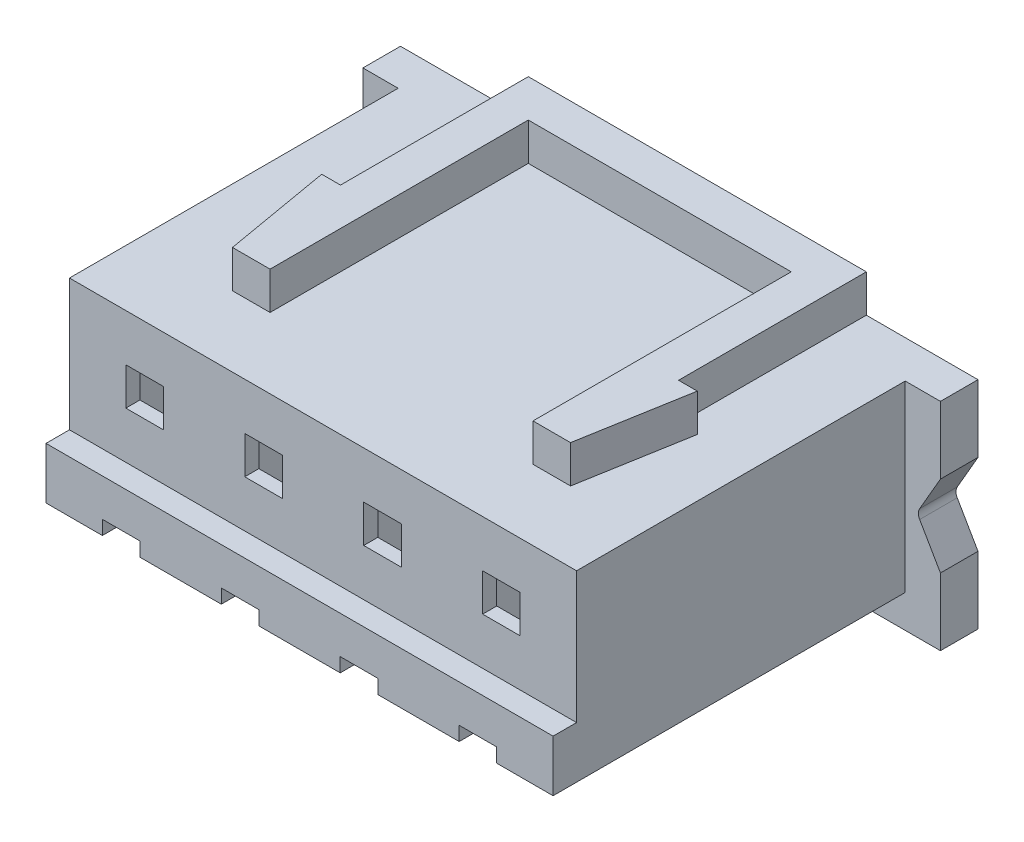
SolidWorks part; units mm, degrees
ref_plane "Front Plane" through (0, 0, 0) normal (0, 0, 1) x (1, 0, 0)
ref_plane "Top Plane" through (0, 0, 0) normal (0, 1, 0) x (1, 0, 0)
ref_plane "Right Plane" through (0, 0, 0) normal (1, 0, 0) x (0, 0, -1)
sketch "Sketch1" plane through (0, 0, 0) normal (0, 0, 1) x (1, 0, 0)
  line L1 (-5.4, -2.15) -> (5.4, -2.15)
  line L2 (-5.4, -2.15) -> (-5.4, 2.15)
  line L3 (-5.4, 2.15) -> (5.4, 2.15)
  line L4 (5.4, -2.15) -> (5.4, 2.15)
  line L5 (-5.4, -2.15) -> (5.4, 2.15) construction
  line L6 (-5.4, 2.15) -> (5.4, -2.15) construction
  point P0 (0, 0)
  dimension "D1" = 4.3
  dimension "D2" = 10.8
extrude "Boss-Extrude1" add sketch "Sketch1" along normal blind 7
sketch "Sketch2" plane through (0, 0, 0) normal (0, 0, -1) x (-1, 0, 0)
  line L0 (0, 0) -> (0, 2.15) construction
  line L1 (-6.15, 2.15) -> (6.15, 2.15)
  line L2 (-6.15, 2.15) -> (-6.15, -2.45)
  line L3 (-6.15, -2.45) -> (6.15, -2.45)
  line L4 (6.15, 2.15) -> (6.15, -2.45)
  dimension "D1" = 12.3
  dimension "D2" = 4.6
extrude "Boss-Extrude2" add sketch "Sketch2" along normal blind 0.8
sketch "Sketch3" plane through (0, 0, 0) normal (0, 0, 1) x (1, 0, 0)
  line L1 (6.15, 2.15) -> (6.15, -2.45) construction
  line L2 (5.65, -0.15) -> (6.15, -1.016)
  line L3 (5.65, -0.15) -> (6.15, 0.716)
  line L4 (6.15, -0.15) -> (5.65, -0.15) construction
  line L5 (6.15, 0.716) -> (6.15, -1.016)
  dimension "D1" = 60
  dimension "D2" = 0.5
  dimension "D3" = 60
extrude "Cut-Extrude1" cut sketch "Sketch3" against normal blind 1
fillet "Fillet1" radius 0.2 1 edges at (5.65, -0.15, -0.4)
sketch "Sketch4" plane through (0, 0, 7) normal (0, 0, 1) x (1, 0, 0)
  line L0 (-5.4, 2.15) -> (-5.4, -2.15) construction
  line L1 (-5.4, -0.65) -> (5.4, -0.65)
  line L2 (-5.4, -0.65) -> (-5.4, -2.15)
  line L3 (-5.4, -2.15) -> (5.4, -2.15)
  line L4 (5.4, -0.65) -> (5.4, -2.15)
  dimension "D1" = 1.5
extrude "Boss-Extrude3" add sketch "Sketch4" along normal blind 0.5
sketch "Sketch5" plane through (0, 0, 7.5) normal (0, 0, 1) x (1, 0, 0)
  line L0 (-5.4, -2.15) -> (5.4, -2.15) construction
  line L1 (-4.2, -1.45) -> (-3.4, -1.45)
  line L2 (-4.2, -1.45) -> (-4.2, -2.15)
  line L3 (-4.2, -2.15) -> (-3.4, -2.15)
  line L4 (-3.4, -1.45) -> (-3.4, -2.15)
  line L5 (-5.4, -0.65) -> (-5.4, -2.15) construction
  line L6 (-1.6667, -1.45) -> (-0.8667, -1.45)
  line L7 (-0.8667, -1.45) -> (-0.8667, -2.15)
  line L8 (-1.6667, -1.45) -> (-1.6667, -2.15)
  line L9 (-1.6667, -2.15) -> (-0.8667, -2.15)
  line L10 (0.8667, -1.45) -> (1.6667, -1.45)
  line L11 (1.6667, -1.45) -> (1.6667, -2.15)
  line L12 (0.8667, -1.45) -> (0.8667, -2.15)
  line L13 (0.8667, -2.15) -> (1.6667, -2.15)
  line L14 (3.4, -1.45) -> (4.2, -1.45)
  line L15 (4.2, -1.45) -> (4.2, -2.15)
  line L16 (3.4, -1.45) -> (3.4, -2.15)
  line L17 (3.4, -2.15) -> (4.2, -2.15)
  line L18 (5.4, -2.15) -> (5.4, -0.65) construction
  line L19 (-5.4, -2.15) -> (5.4, -2.15) construction
  dimension "D1" = 0.8
  dimension "D2" = 1.2
  dimension "D3" = 0.7
  dimension "D5" = 1.2
  dimension "D6" = 0.7
  dimension "D4" = 4
extrude "Cut-Extrude2" cut sketch "Sketch5" against normal blind 3.2
sketch "Sketch6" plane through (0, 0, 7) normal (0, 0, 1) x (1, 0, 0)
  line L0 (-5.4, 2.15) -> (-5.4, -0.65) construction
  line L1 (-4.2, 1.15) -> (-3.4, 1.15)
  line L2 (-4.2, 1.15) -> (-4.2, 0.35)
  line L3 (-4.2, 0.35) -> (-3.4, 0.35)
  line L4 (-3.4, 1.15) -> (-3.4, 0.35)
  line L5 (-1.6667, 0.35) -> (-0.8667, 0.35)
  line L6 (-0.8667, 1.15) -> (-0.8667, 0.35)
  line L7 (-1.6667, 1.15) -> (-0.8667, 1.15)
  line L8 (-1.6667, 1.15) -> (-1.6667, 0.35)
  line L9 (0.8667, 0.35) -> (1.6667, 0.35)
  line L10 (1.6667, 1.15) -> (1.6667, 0.35)
  line L11 (0.8667, 1.15) -> (1.6667, 1.15)
  line L12 (0.8667, 1.15) -> (0.8667, 0.35)
  line L13 (3.4, 0.35) -> (4.2, 0.35)
  line L14 (4.2, 1.15) -> (4.2, 0.35)
  line L15 (3.4, 1.15) -> (4.2, 1.15)
  line L16 (3.4, 1.15) -> (3.4, 0.35)
  line L17 (5.4, -2.15) -> (5.4, 2.15) construction
  line L18 (5.4, 2.15) -> (-5.4, 2.15) construction
  dimension "D1" = 0.8
  dimension "D2" = 0.8
  dimension "D3" = 1.2
  dimension "D5" = 1.2
  dimension "D6" = 1
  dimension "D7" = 1
  dimension "D4" = 4
extrude "Cut-Extrude3" cut sketch "Sketch6" against normal blind 10
sketch "Sketch7" plane through (0, 2.15, 0) normal (0, 1, 0) x (1, 0, 0)
  line L0 (-3.428, -5.5) -> (-3.828, -3.2)
  line L1 (-3.828, -3.2) -> (-3.428, -3.2)
  line L2 (-3.428, -3.2) -> (-3.428, 0.8)
  line L3 (-6.15, 0.8) -> (6.15, 0.8) construction
  line L4 (-3.428, 0.8) -> (3.772, 0.8)
  line L5 (3.772, 0.8) -> (3.772, -3.2)
  line L6 (3.772, -3.2) -> (4.172, -3.2)
  line L7 (4.172, -3.2) -> (3.772, -5.5)
  line L8 (3.772, -5.5) -> (2.972, -5.5)
  line L9 (2.972, -5.5) -> (2.972, 0)
  line L10 (2.972, 0) -> (-2.628, 0)
  line L11 (-2.628, 0) -> (-2.628, -5.5)
  line L12 (-2.628, -5.5) -> (-3.428, -5.5)
  dimension "D1" = 0.8
  dimension "D2" = 0.8
  dimension "D3" = 0.8
  dimension "D4" = 0.8
  dimension "D5" = 1.2
  dimension "D6" = 4
  dimension "D7" = 2.3
  dimension "D8" = 4
  dimension "D9" = 1.2
  dimension "D10" = 0.8
  dimension "D11" = 8
extrude "Boss-Extrude4" add sketch "Sketch7" along normal blind 0.8
sketch "Sketch8" plane through (0, 0, -0.8) normal (0, 0, -1) x (-1, 0, 0)
  line L0 (3.4, -1.45) -> (4.2, -1.45) construction
  line L1 (4.9, 1.75) -> (2.7, 1.75)
  line L2 (4.9, 1.75) -> (4.9, -1.05)
  line L3 (4.2, -1.45) -> (3.4, -1.45)
  line L4 (2.7, 1.75) -> (2.7, -1.05)
  line L5 (4.9, -1.05) -> (4.2, -1.05)
  line L6 (4.2, -1.05) -> (4.2, -1.45)
  line L7 (3.4, -1.45) -> (3.4, -1.05)
  line L8 (3.4, -1.05) -> (2.7, -1.05)
  line L9 (-0.8667, -1.45) -> (-0.8667, -2.15) construction
  line L11 (0.1667, 1.75) -> (0.1667, -1.05)
  line L12 (0.8667, -1.05) -> (0.1667, -1.05)
  line L13 (0.8667, -1.45) -> (0.8667, -1.05)
  line L14 (1.6667, -1.45) -> (0.8667, -1.45)
  line L15 (2.3667, -1.05) -> (1.6667, -1.05)
  line L16 (1.6667, -1.05) -> (1.6667, -1.45)
  line L17 (2.3667, 1.75) -> (2.3667, -1.05)
  line L18 (2.3667, 1.75) -> (0.1667, 1.75)
  line L19 (-2.3667, 1.75) -> (-2.3667, -1.05)
  line L20 (-1.6667, -1.05) -> (-2.3667, -1.05)
  line L21 (-1.6667, -1.45) -> (-1.6667, -1.05)
  line L22 (-0.8667, -1.45) -> (-1.6667, -1.45)
  line L23 (-0.1633, -1.05) -> (-0.8667, -1.05)
  line L24 (-0.8667, -1.05) -> (-0.8667, -1.45)
  line L25 (-0.1633, 1.75) -> (-0.1633, -1.05)
  line L26 (-0.1633, 1.75) -> (-2.3667, 1.75)
  line L27 (-4.9, 1.75) -> (-4.9, -1.05)
  line L28 (-4.2, -1.05) -> (-4.9, -1.05)
  line L29 (-4.2, -1.45) -> (-4.2, -1.05)
  line L30 (-3.4, -1.45) -> (-4.2, -1.45)
  line L31 (-2.7, -1.05) -> (-3.4, -1.05)
  line L32 (-3.4, -1.05) -> (-3.4, -1.45)
  line L33 (-2.7, 1.75) -> (-2.7, -1.05)
  line L34 (-2.7, 1.75) -> (-4.9, 1.75)
  line L36 (1.6667, -1.45) -> (1.6667, -2.15) construction
  dimension "D1" = 2.8
  dimension "D2" = 2.2
  dimension "D3" = 0.4
  dimension "D4" = 0.4
  dimension "D5" = 0.7
  dimension "D6" = 0.7
  dimension "D8" = 0.7
  dimension "D9" = 0.3333
  dimension "D7" = 2.2
  dimension "D10" = 0.7
  dimension "D11" = 0.4
  dimension "D12" = 2.8
  dimension "D13" = 0.33
  dimension "D14" = 2.2
  dimension "D15" = 0.7
  dimension "D16" = 0.7
  dimension "D17" = 0.4
  dimension "D18" = 0.3333
extrude "Cut-Extrude4" cut sketch "Sketch8" against normal blind 7.5
sketch "Sketch9" plane through (0, -2.15, 0) normal (0, -1, 0) x (1, 0, 0)
  line L20 (4.2, 4.3) -> (3.4, 4.3)
  line L21 (3.4, 4.3) -> (3.4, 7.5)
  line L22 (3.4, 7.5) -> (1.6667, 7.5)
  line L23 (1.6667, 7.5) -> (1.6667, 4.3)
  line L24 (1.6667, 4.3) -> (0.8667, 4.3)
  line L25 (0.8667, 4.3) -> (0.8667, 7.5)
  line L26 (0.8667, 7.5) -> (-0.8667, 7.5)
  line L27 (-0.8667, 7.5) -> (-0.8667, 4.3)
  line L28 (-0.8667, 4.3) -> (-1.6667, 4.3)
  line L29 (-1.6667, 4.3) -> (-1.6667, 7.5)
  line L30 (-1.6667, 7.5) -> (-3.4, 7.5)
  line L31 (-3.4, 7.5) -> (-3.4, 4.3)
  line L32 (-3.4, 4.3) -> (-4.2, 4.3)
  line L33 (-4.2, 4.3) -> (-4.2, 7.5)
  line L34 (-4.2, 7.5) -> (-5.4, 7.5)
  line L35 (-5.4, 7.5) -> (-5.4, 0)
  line L36 (-5.4, 0) -> (5.4, 0)
  line L37 (5.4, 0) -> (5.4, 7.5)
  line L38 (5.4, 7.5) -> (4.2, 7.5)
  line L39 (4.2, 7.5) -> (4.2, 4.3)
  line L40 (4.2, 4.3) -> (3.4, 4.3)
  line L41 (3.4, 4.3) -> (3.4, 7.5)
  line L42 (3.4, 7.5) -> (1.6667, 7.5)
  line L43 (1.6667, 7.5) -> (1.6667, 4.3)
  line L44 (1.6667, 4.3) -> (0.8667, 4.3)
  line L45 (0.8667, 4.3) -> (0.8667, 7.5)
  line L46 (0.8667, 7.5) -> (-0.8667, 7.5)
  line L47 (-0.8667, 7.5) -> (-0.8667, 4.3)
  line L48 (-0.8667, 4.3) -> (-1.6667, 4.3)
  line L49 (-1.6667, 4.3) -> (-1.6667, 7.5)
  line L50 (-1.6667, 7.5) -> (-3.4, 7.5)
  line L51 (-3.4, 7.5) -> (-3.4, 4.3)
  line L52 (-3.4, 4.3) -> (-4.2, 4.3)
  line L53 (-4.2, 4.3) -> (-4.2, 7.5)
  line L54 (-4.2, 7.5) -> (-5.4, 7.5)
  line L55 (-5.4, 7.5) -> (-5.4, 0)
  line L56 (-5.4, 0) -> (5.4, 0)
  line L57 (5.4, 0) -> (5.4, 7.5)
  line L58 (5.4, 7.5) -> (4.2, 7.5)
  line L59 (4.2, 7.5) -> (4.2, 4.3)
  dimension "D1" = 0
extrude "Cut-Extrude5" cut sketch "Sketch9" against normal blind 0.4
sketch "Sketch10" plane through (0, 0, -0.8) normal (0, 0, -1) x (-1, 0, 0)
  line L0 (-5.4156, -2.1633) -> (5.5527, -2.1633) construction
  text T0 "       1           2            3           4" font "Century Gothic" height 0.5
extrude "Boss-Extrude5" add sketch "Sketch10" along normal blind 0.1
